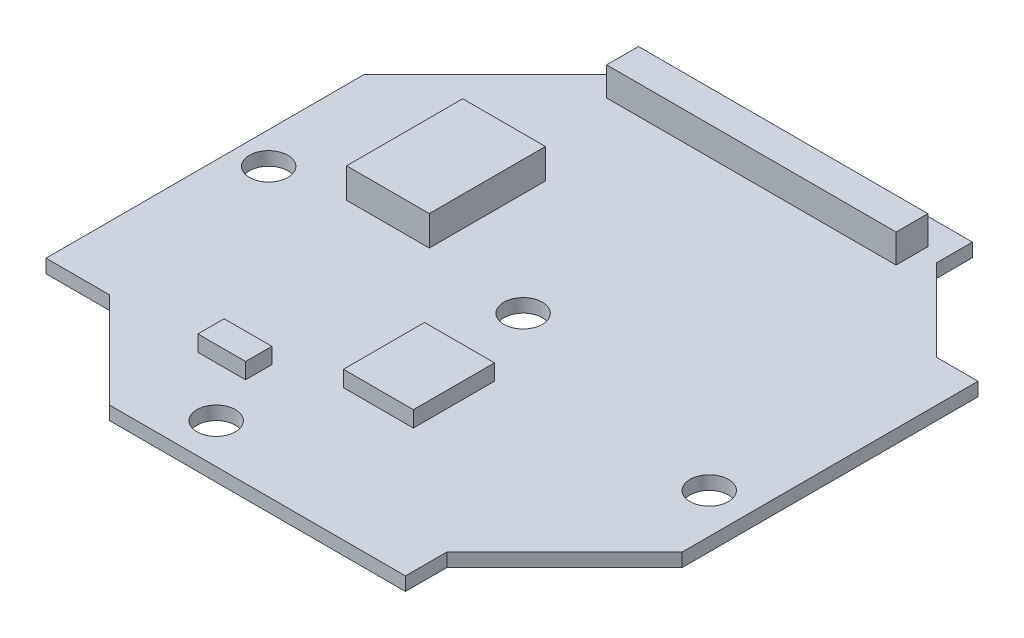
SolidWorks part; units mm, degrees
ref_plane "Front Plane" through (0, 0, 0) normal (0, 0, 1) x (1, 0, 0)
ref_plane "Top Plane" through (0, 0, 0) normal (0, 1, 0) x (1, 0, 0)
ref_plane "Right Plane" through (0, 0, 0) normal (1, 0, 0) x (0, 0, -1)
sketch "Sketch1" plane through (0, 0, 0) normal (0, 1, 0) x (1, 0, 0)
  line L0 (-10.25, 18) -> (10.25, 18)
  line L1 (10.25, 18) -> (10.25, 15.75)
  line L2 (10.25, 15.75) -> (15.4, 10.6)
  line L3 (15.4, 10.6) -> (18, 10.6)
  line L4 (18, 10.6) -> (18, -8)
  line L5 (18, -8) -> (10.6, -15.4)
  line L6 (10.6, -15.4) -> (10.6, -18)
  line L7 (10.6, -18) -> (-8, -18)
  line L8 (-8, -18) -> (-14, -12)
  line L9 (-14, -12) -> (-18, -12)
  line L10 (-18, -12) -> (-18, 8)
  line L11 (-18, 8) -> (-10.25, 15.75)
  line L12 (-10.25, 15.75) -> (-10.25, 18)
  line L13 (0, 0) -> (0, 18) construction
  line L14 (0, 0) -> (-18, 0) construction
  line L15 (0, 0) -> (18, 0) construction
  line L16 (0, 0) -> (0, -18) construction
  dimension "D1" = 18
  dimension "D2" = 2.25
  dimension "D3" = 2.6
  dimension "D4" = 10.25
  dimension "D5" = 45
  dimension "D6" = 4
  dimension "D7" = 2.6
  dimension "D8" = 12
  dimension "D9" = 10.6
extrude "Boss-Extrude1" add sketch "Sketch1" along normal blind 0.85
sketch "Sketch2" plane through (0, 0.85, 0) normal (0, 1, 0) x (1, 0, 0)
  line L0 (-9.1, 15.35) -> (9.1, 15.35) construction
  line L1 (-9.1, 16.35) -> (9.1, 16.35)
  line L2 (-9.1, 16.35) -> (-9.1, 14.35)
  line L3 (-9.1, 14.35) -> (9.1, 14.35)
  line L4 (9.1, 16.35) -> (9.1, 14.35)
  line L5 (0, 15.35) -> (0, 0) construction
  dimension "D1" = 2
  dimension "D2" = 18.2
  dimension "D3" = 15.35
extrude "Boss-Extrude2" add sketch "Sketch2" along normal blind 1.8
sketch "Sketch3" plane through (0, 0.85, 0) normal (0, 1, 0) x (1, 0, 0)
  line L1 (-11.7, 7.9) -> (-6.5, 7.9)
  line L2 (-11.7, 7.9) -> (-11.7, 0.6)
  line L3 (-11.7, 0.6) -> (-6.5, 0.6)
  line L4 (-6.5, 7.9) -> (-6.5, 0.6)
  dimension "D1" = 7.3
  dimension "D2" = 5.2
  dimension "D3" = 6.5
  dimension "D4" = 0.6
extrude "Boss-Extrude3" add sketch "Sketch3" along normal blind 1.88
sketch "Sketch4" plane through (0, 0.85, 0) normal (0, 1, 0) x (1, 0, 0)
  line L1 (-1.6, -4.6) -> (2.8, -4.6)
  line L2 (-1.6, -4.6) -> (-1.6, -9.7)
  line L3 (-1.6, -9.7) -> (2.8, -9.7)
  line L4 (2.8, -4.6) -> (2.8, -9.7)
  line L5 (-5.1, -12.35) -> (-8.1, -12.35)
  line L6 (-5.1, -12.35) -> (-5.1, -10.7)
  line L7 (-5.1, -10.7) -> (-8.1, -10.7)
  line L8 (-8.1, -12.35) -> (-8.1, -10.7)
  point P4 (0.6, -4.6)
  dimension "D1" = 5.1
  dimension "D2" = 4.4
  dimension "D3" = 4.6
  dimension "D4" = 0.6
  dimension "D5" = 3
  dimension "D6" = 1.65
  dimension "D7" = 3.5
  dimension "D8" = 1
extrude "Boss-Extrude4" add sketch "Sketch4" along normal blind 1
sketch "Sketch5" plane through (0, 0.85, 0) normal (0, 1, 0) x (1, 0, 0)
  circle A0 centre (0, 0) radius 1.21
  circle A1 centre (-16, 0) radius 1.21
  circle A2 centre (-3.8, -15.5) radius 1.21
  circle A3 centre (15.5, -3.8) radius 1.21
  dimension "D1" = 2.42
  dimension "D5" = 15.5
  dimension "D2" = 16
  dimension "D3" = 15.5
  dimension "D4" = 3.8
  dimension "D6" = 3.8
extrude "Cut-Extrude1" cut sketch "Sketch5" against normal through all
